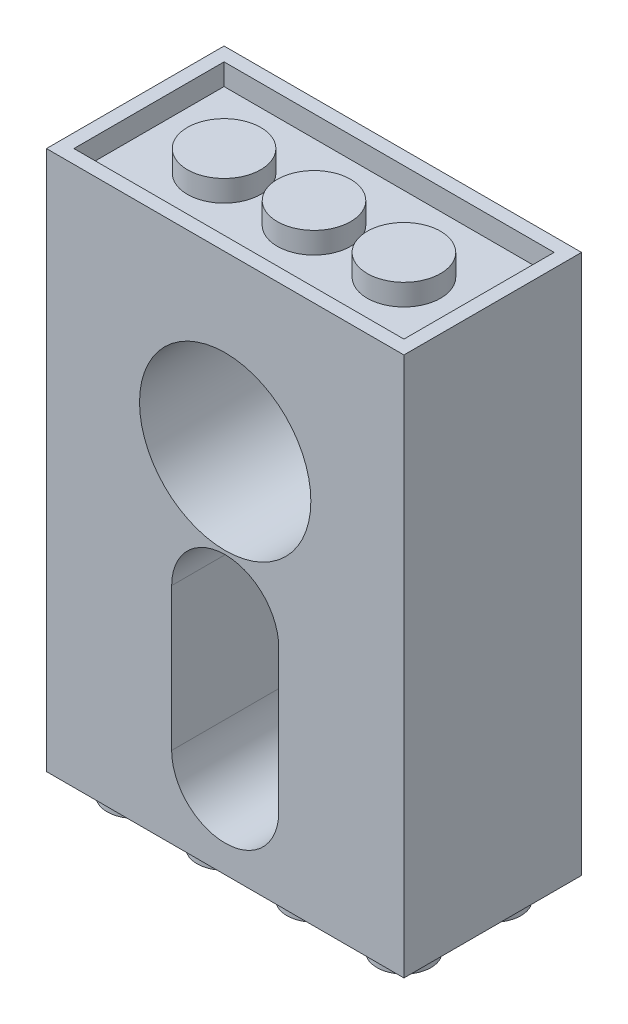
SolidWorks part; units mm, degrees
ref_plane "Front Plane" through (0, 0, 0) normal (0, 0, 1) x (1, 0, 0)
ref_plane "Top Plane" through (0, 0, 0) normal (0, 1, 0) x (1, 0, 0)
ref_plane "Right Plane" through (0, 0, 0) normal (1, 0, 0) x (0, 0, -1)
sketch "Sketch1" plane through (0, 0, 0) normal (0, 0, 1) x (1, 0, 0)
  line L1 (-15.9, 24) -> (15.9, 24)
  line L2 (-15.9, 24) -> (-15.9, -24)
  line L3 (-15.9, -24) -> (15.9, -24)
  line L4 (15.9, 24) -> (15.9, -24)
  line L5 (-15.9, 24) -> (15.9, -24) construction
  line L6 (-15.9, -24) -> (15.9, 24) construction
  point P0 (0, 0)
  dimension "D1" = 48
  dimension "D2" = 31.8
extrude "Boss-Extrude1" add sketch "Sketch1" along normal blind 15.8
sketch "Sketch2" plane through (0, 0, 15.8) normal (0, 0, 1) x (1, 0, 0)
  line L0 (0, -4.1) -> (0, -16.8) construction
  line L1 (4.7625, -4.1) -> (4.7625, -16.8)
  line L2 (-4.7625, -4.1) -> (-4.7625, -16.8)
  line L3 (15.9, 24) -> (-15.9, 24) construction
  line L5 (15.9, -24) -> (15.9, 24) construction
  circle A0 centre (0, 8.6) radius 7.62
  arc A1 (4.7625, -4.1) -> (-4.7625, -4.1) centre (0, -4.1) ccw
  arc A2 (-4.7625, -16.8) -> (4.7625, -16.8) centre (0, -16.8) ccw
  point P5 (0, -10.45)
  dimension "D1" = 4.7625
  dimension "D4" = 15.24
  dimension "D2" = 12.7
  dimension "D3" = 12.7
  dimension "D5" = 15.4
  dimension "D6" = 15.9
extrude "Cut-Extrude1" cut sketch "Sketch2" against normal blind 12.7
sketch "Sketch3" plane through (0, 0, 0) normal (0, 0, -1) x (-1, 0, 0)
  line L0 (-15.9, 24) -> (15.9, 24) construction
  circle A6 centre (0, 8.6) radius 2.7782
  circle A7 centre (0, -4.1) radius 1.8415
  circle A8 centre (0, -16.8) radius 1.8415
  dimension "D1" = 5.5563
  dimension "D2" = 3.683
  dimension "D3" = 3.683
  dimension "D4" = 15.4
  dimension "D5" = 12.7
  dimension "D6" = 12.7
extrude "Cut-Extrude2" cut sketch "Sketch3" against normal blind 12.7
sketch "Sketch4" plane through (0, 0, 0) normal (0, 0, -1) x (-1, 0, 0)
  line L2 (4.7625, -16.8) -> (4.7625, -4.1)
  line L3 (-4.7625, -4.1) -> (-4.7625, -16.8)
  line L12 (4.7625, -16.8) -> (4.7625, -4.1)
  line L13 (-4.7625, -4.1) -> (-4.7625, -16.8)
  arc A2 (4.7625, -4.1) -> (-4.7625, -4.1) centre (0, -4.1) ccw
  arc A3 (-4.7625, -16.8) -> (4.7625, -16.8) centre (0, -16.8) ccw
  arc A4 (4.7625, -4.1) -> (-4.7625, -4.1) centre (0, -4.1) ccw
  arc A5 (-4.7625, -16.8) -> (4.7625, -16.8) centre (0, -16.8) ccw
  dimension "D2" = 0
extrude "Cut-Extrude3" cut sketch "Sketch4" against normal blind 1.905
sketch "Sketch5" plane through (0, -24, 0) normal (0, -1, 0) x (1, 0, 0)
  line L0 (-15.9, 15.8) -> (15.9, 15.8) construction
  line L1 (-15.9, 15.8) -> (-15.9, 0) construction
  circle A0 centre (-12, 11.9) radius 2.4
  circle A1 centre (-12, 3.9) radius 2.4
  circle A2 centre (-4, 11.9) radius 2.4
  circle A3 centre (-4, 3.9) radius 2.4
  circle A4 centre (4, 11.9) radius 2.4
  circle A5 centre (4, 3.9) radius 2.4
  circle A6 centre (12, 11.9) radius 2.4
  circle A7 centre (12, 3.9) radius 2.4
  dimension "D1" = 4.8
  dimension "D2" = 4.8
  dimension "D3" = 8
  dimension "D4" = 3.9
  dimension "D5" = 3.9
  dimension "D6" = 3.9
  dimension "D7" = 4
extrude "Boss-Extrude2" add sketch "Sketch5" along normal blind 1.905
sketch "Sketch6" plane through (0, 24, 0) normal (0, 1, 0) x (1, 0, 0)
  line L0 (15.9, 0) -> (-15.9, 0) construction
  line L1 (-14.68, -14.58) -> (14.68, -14.58)
  line L2 (-14.68, -14.58) -> (-14.68, -1.22)
  line L3 (-14.68, -1.22) -> (14.68, -1.22)
  line L4 (14.68, -14.58) -> (14.68, -1.22)
  line L5 (-15.9, -15.8) -> (-15.9, 0) construction
  line L6 (15.9, -15.8) -> (-15.9, -15.8) construction
  line L7 (15.9, -15.8) -> (15.9, 0) construction
  circle A0 centre (-8, -7.9) radius 3.2605
  circle A1 centre (0, -7.9) radius 3.2605
  circle A2 centre (8, -7.9) radius 3.2605
  dimension "D5" = 6.521
  dimension "D1" = 1.22
  dimension "D2" = 1.22
  dimension "D3" = 1.22
  dimension "D4" = 1.22
  dimension "D6" = 7.9
  dimension "D7" = 7.9
  dimension "D8" = 3
extrude "Cut-Extrude4" cut sketch "Sketch6" against normal blind 1.905
